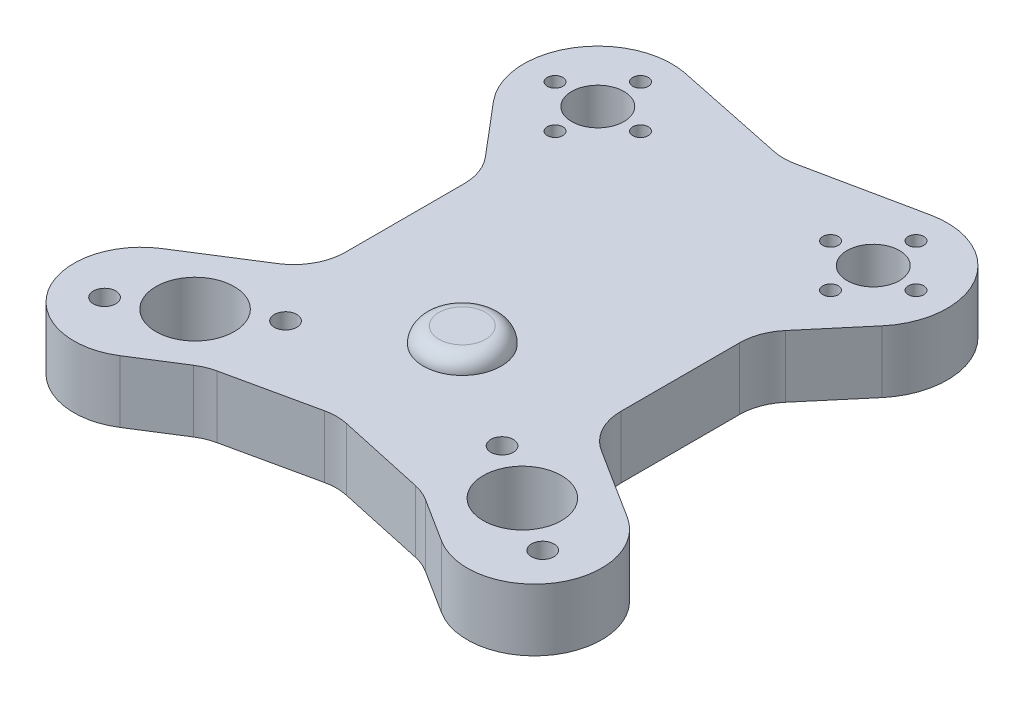
SolidWorks part; units mm, degrees
ref_plane "Front Plane" through (0, 0, 0) normal (0, 0, 1) x (1, 0, 0)
ref_plane "Top Plane" through (0, 0, 0) normal (0, 1, 0) x (1, 0, 0)
ref_plane "Right Plane" through (0, 0, 0) normal (1, 0, 0) x (0, 0, -1)
sketch "Sketch1" plane through (0, 0, 0) normal (0, 1, 0) x (1, 0, 0)
  line L0 (0, -78.0652) -> (0, 78.0652) construction
  line L1 (-42.2865, -26.7721) -> (-20.8935, -13.2279) construction
  line L2 (-2.0365, 62.2326) -> (-23.679, 66.7345)
  line L3 (-37.5049, 43.5105) -> (-28.954, 33.3983)
  line L4 (-26.59, 26.9413) -> (-26.59, 4.037)
  line L5 (-31.2408, -4.412) -> (-44.9142, -13.0688)
  line L6 (-31.0239, -35.0085) -> (-44.9142, -13.0688) construction
  line L7 (-31.0239, -35.0085) -> (-22.3861, -29.5398)
  line L8 (-19.1675, -28.2185) -> (-2.1306, -24.5033)
  line L9 (31.0239, -35.0085) -> (44.9142, -13.0688) construction
  line L10 (42.2865, -26.7721) -> (20.8935, -13.2279) construction
  line L11 (19.1675, -28.2185) -> (2.1306, -24.5033)
  line L12 (31.0239, -35.0085) -> (22.3861, -29.5398)
  line L13 (31.2408, -4.412) -> (44.9142, -13.0688)
  line L14 (26.59, 26.9413) -> (26.59, 4.037)
  line L15 (37.5049, 43.5105) -> (28.954, 33.3983)
  line L16 (2.0365, 62.2326) -> (23.679, 66.7345)
  circle A0 centre (0, 0) radius 5.15
  circle A1 centre (-31.59, -20) radius 7.55
  circle A3 centre (-26.59, 52.74) radius 5.05
  circle A4 centre (-26.59, 52.74) radius 11 construction
  circle A5 centre (-26.59, 52.74) radius 8.25 construction
  circle A6 centre (-26.59, 60.99) radius 1.5
  circle A7 centre (-18.34, 52.74) radius 1.5
  circle A8 centre (-26.59, 44.49) radius 1.5
  circle A9 centre (-34.84, 52.74) radius 1.5
  circle A10 centre (-42.2865, -26.7721) radius 2.165
  circle A11 centre (-20.8935, -13.2279) radius 2.165
  arc A12 (-23.679, 66.7345) -> (-37.5049, 43.5105) centre (-26.59, 52.74) ccw
  arc A13 (-44.9142, -13.0688) -> (-31.0239, -35.0085) centre (-37.969, -24.0386) ccw
  arc A14 (-22.3861, -29.5398) -> (-19.1675, -28.2185) centre (-17.0369, -37.9889) cw
  arc A15 (-28.954, 33.3983) -> (-26.59, 26.9413) centre (-36.59, 26.9413) cw
  arc A16 (-26.59, 4.037) -> (-31.2408, -4.412) centre (-36.59, 4.037) cw
  circle A17 centre (26.59, 52.74) radius 8.25 construction
  circle A18 centre (26.59, 52.74) radius 11 construction
  arc A19 (26.59, 4.037) -> (31.2408, -4.412) centre (36.59, 4.037) ccw
  arc A20 (28.954, 33.3983) -> (26.59, 26.9413) centre (36.59, 26.9413) ccw
  arc A21 (22.3861, -29.5398) -> (19.1675, -28.2185) centre (17.0369, -37.9889) ccw
  arc A22 (44.9142, -13.0688) -> (31.0239, -35.0085) centre (37.969, -24.0386) cw
  arc A23 (23.679, 66.7345) -> (37.5049, 43.5105) centre (26.59, 52.74) cw
  circle A24 centre (20.8935, -13.2279) radius 2.165
  circle A25 centre (42.2865, -26.7721) radius 2.165
  circle A26 centre (34.84, 52.74) radius 1.5
  circle A27 centre (26.59, 44.49) radius 1.5
  circle A28 centre (18.34, 52.74) radius 1.5
  circle A29 centre (26.59, 60.99) radius 1.5
  circle A30 centre (26.59, 52.74) radius 5.05
  circle A31 centre (31.59, -20) radius 7.55
  arc A32 (-2.1306, -24.5033) -> (2.1306, -24.5033) centre (0, -34.2736) cw
  arc A33 (-2.0365, 62.2326) -> (2.0365, 62.2326) centre (0, 72.0231) ccw
  point P10 (0, 0)
  point P23 (-26.59, 52.74)
  point P25 (-31.59, -20)
  point P76 (31.59, -20)
  point P77 (26.59, 52.74)
  point P80 (0, -24.0386)
  point P83 (0, 61.809)
  dimension "D1" = 10.3
  dimension "D2" = 10.1
  dimension "D3" = 3
  dimension "D4" = 15.1
  dimension "D5" = 4
  dimension "D6" = 16.5
  dimension "D7" = 22
  dimension "D9" = 4.33
  dimension "D14" = 10
  dimension "D15" = 10
  dimension "D8" = 25.32
  dimension "D10" = 31.59
  dimension "D11" = 20
  dimension "D12" = 52.74
  dimension "D13" = 26.59
extrude "Boss-Extrude1" add sketch "Sketch1" along normal blind 12
sketch "Sketch2" plane through (0, 0, 0) normal (1, 0, 0) x (0, 0, -1)
  line L0 (0, 0) -> (0, 15) construction
  line L1 (7.5, 15) -> (-7.5, 15)
  line L2 (-7.5, 15) -> (-7.5, 10)
  line L3 (-7.5, 10) -> (7.5, 10)
  line L4 (7.5, 10) -> (7.5, 15)
  line L5 (4.037, 0) -> (26.9413, 0) construction
  point P6 (0, 15)
  dimension "D1" = 10
  dimension "D2" = 5
  dimension "D3" = 15
revolve "Revolve1" add sketch "Sketch2" angle 360 about L0
fillet "Fillet1" radius 3 1 edges at (0, 15, -7.5)
